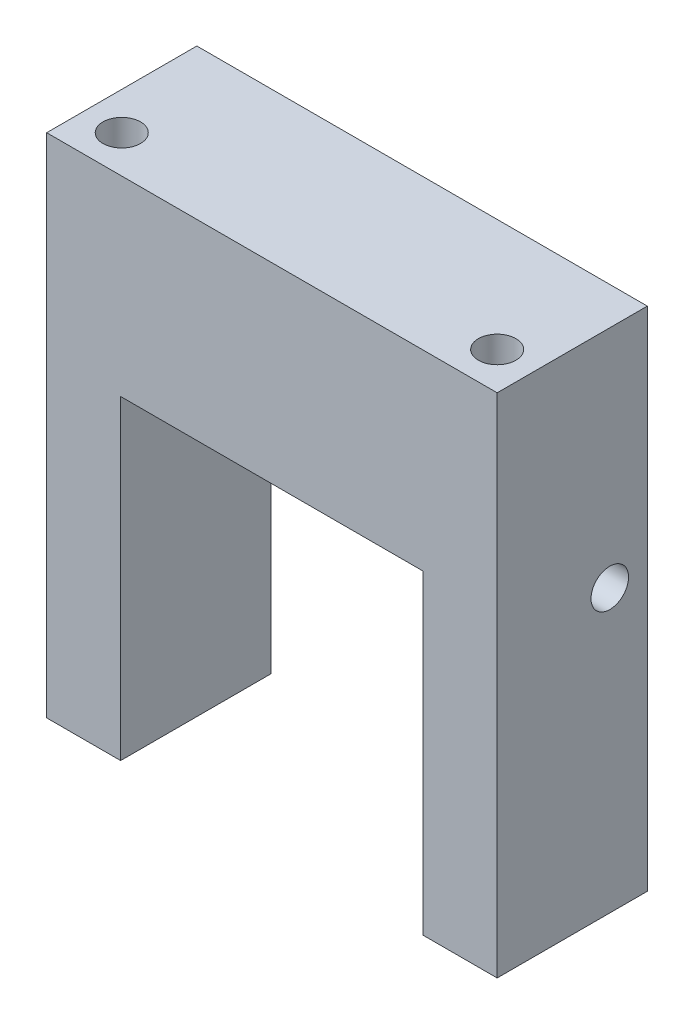
SolidWorks part; units mm, degrees
ref_plane "Front Plane" through (0, 0, 0) normal (0, 0, 1) x (1, 0, 0)
ref_plane "Top Plane" through (0, 0, 0) normal (0, 1, 0) x (1, 0, 0)
ref_plane "Right Plane" through (0, 0, 0) normal (1, 0, 0) x (0, 0, -1)
sketch "Sketch1" plane through (0, 0, 0) normal (0, 0, 1) x (1, 0, 0)
  line L0 (50.15, 0) -> (60, 0)
  line L1 (0, 0) -> (9.85, 0)
  line L2 (0, 0) -> (0, 67.5)
  line L3 (0, 67.5) -> (60, 67.5)
  line L4 (60, 0) -> (60, 67.5)
  line L6 (9.85, 0) -> (9.85, 42)
  line L7 (9.85, 42) -> (50.15, 42)
  line L8 (50.15, 0) -> (50.15, 42)
  point P9 (30, 42)
  point P10 (30, 67.5)
  dimension "D1" = 40.3
  dimension "D2" = 42
  dimension "D3" = 67.5
  dimension "D4" = 60
extrude "Boss-Extrude1" add sketch "Sketch1" along normal blind 20
sketch "Sketch3" plane through (0, 0, 0) normal (0, -1, 0) x (1, 0, 0)
  line L0 (0, 20) -> (0, 0) construction
  line L1 (60, 20) -> (60, 0) construction
  line L2 (0, 20) -> (9.85, 20) construction
  circle A0 centre (5, 15) radius 2.5
  circle A1 centre (55, 15) radius 2.5
  dimension "D1" = 5
  dimension "D3" = 5
  dimension "D4" = 5
  dimension "D5" = 5
extrude "Cut-Extrude1" cut sketch "Sketch3" against normal through all
sketch "Sketch4" plane through (0, 0, 0) normal (-1, 0, 0) x (0, 0, 1)
  line L0 (20, 0) -> (0, 0) construction
  line L1 (0, 67.5) -> (0, 0) construction
  circle A0 centre (5, 37.5) radius 2.5
  dimension "D1" = 5
  dimension "D2" = 37.5
  dimension "D3" = 5
extrude "Cut-Extrude2" cut sketch "Sketch4" against normal through all
